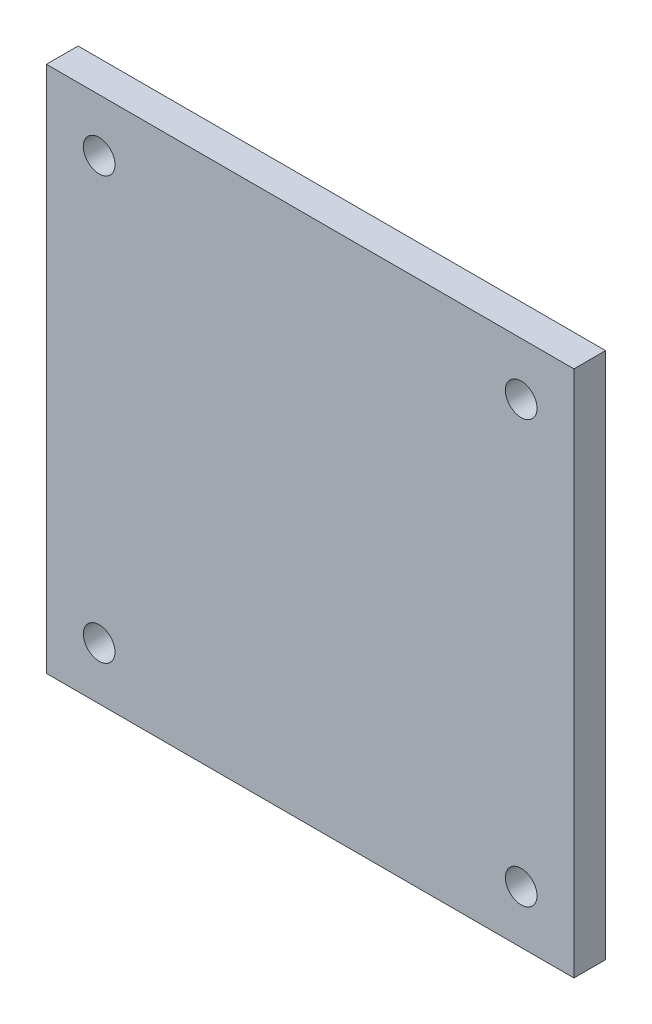
SolidWorks part; units mm, degrees
ref_plane "Front Plane" through (0, 0, 0) normal (0, 0, 1) x (1, 0, 0)
ref_plane "Top Plane" through (0, 0, 0) normal (0, 1, 0) x (1, 0, 0)
ref_plane "Right Plane" through (0, 0, 0) normal (1, 0, 0) x (0, 0, -1)
sketch "Sketch1" plane through (0, 0, 0) normal (0, 0, 1) x (1, 0, 0)
  line L1 (0, 0) -> (50, 0)
  line L2 (0, 0) -> (0, 50)
  line L3 (0, 50) -> (50, 50)
  line L4 (50, 0) -> (50, 50)
  circle A0 centre (5, 45) radius 1.5
  circle A1 centre (45, 45) radius 1.5
  circle A2 centre (45, 5) radius 1.5
  circle A3 centre (5, 5) radius 1.5
  point P7 (25, 25)
  point P9 (0, 25)
  point P10 (25, 50)
  point P19 (25, 25)
  dimension "D3" = 5
  dimension "D4" = 3
  dimension "D6" = 40
  dimension "D1" = 50
  dimension "D2" = 5
  dimension "D5" = 4
extrude "Boss-Extrude1" add sketch "Sketch1" along normal blind 3
